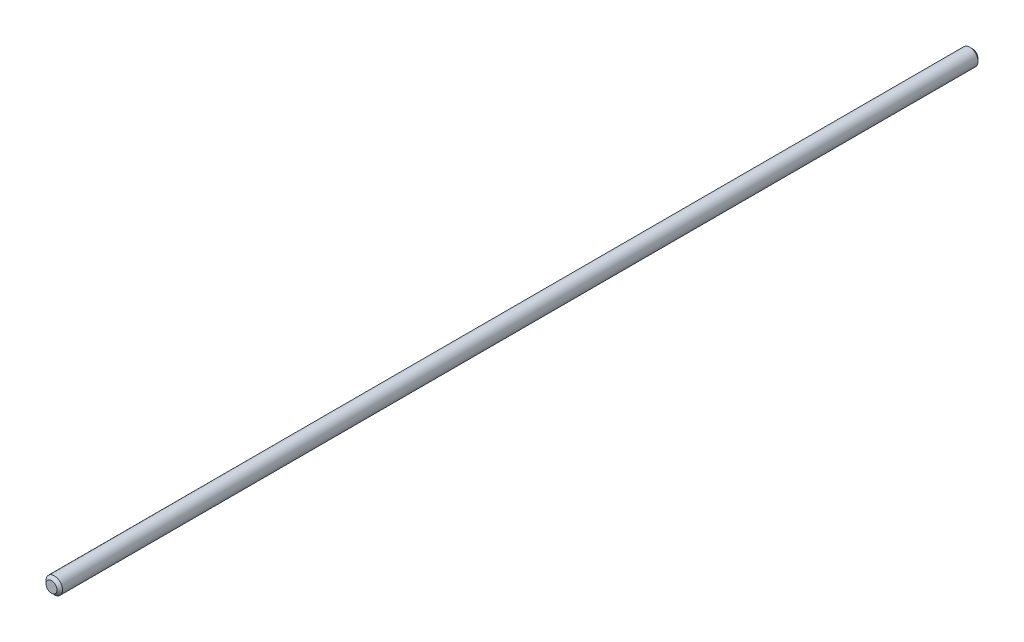
SolidWorks part; units mm, degrees
ref_plane "Plan1" through (0, 0, 0) normal (0, 0, 1) x (1, 0, 0)
ref_plane "Plan2" through (0, 0, 0) normal (0, 1, 0) x (1, 0, 0)
ref_plane "Plan3" through (0, 0, 0) normal (1, 0, 0) x (0, 0, -1)
sketch "Esquisse1" plane through (0, 0, 0) normal (0, 0, 1) x (1, 0, 0)
  circle A0 centre (0, 0) radius 3
  dimension "D1" = 6
extrude "Base-Extrusion" add sketch "Esquisse1" along normal blind 335
chamfer "Chanfrein1" distance 1 angle 45
